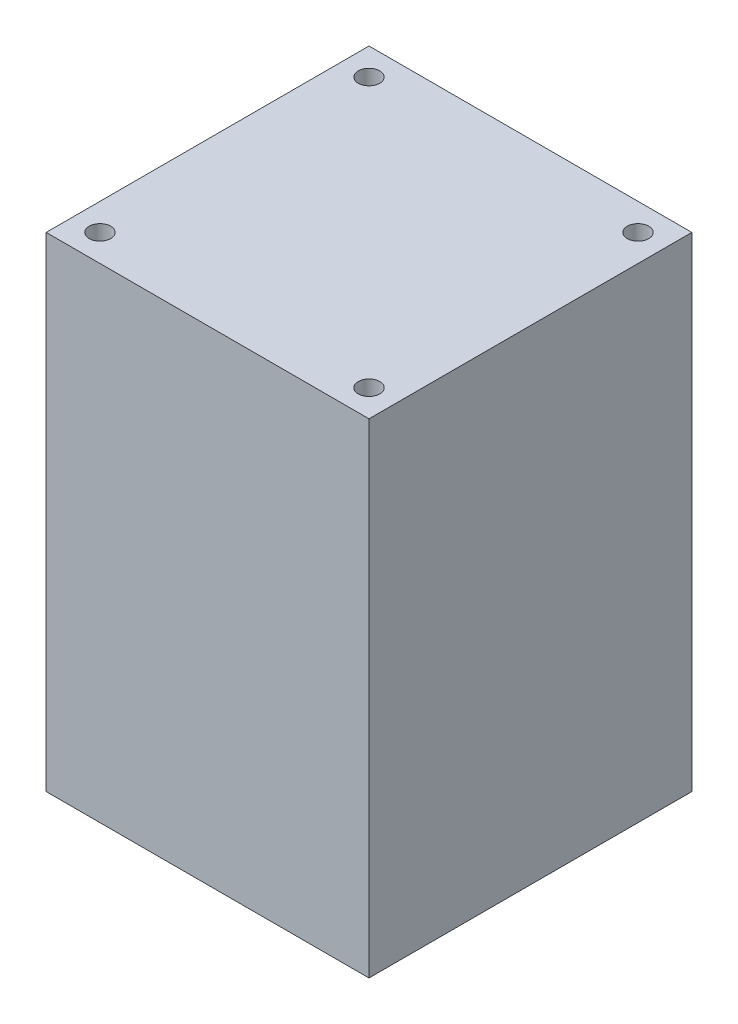
SolidWorks part; units mm, degrees
ref_plane "Front Plane" through (0, 0, 0) normal (0, 0, 1) x (1, 0, 0)
ref_plane "Top Plane" through (0, 0, 0) normal (0, 1, 0) x (1, 0, 0)
ref_plane "Right Plane" through (0, 0, 0) normal (1, 0, 0) x (0, 0, -1)
sketch "Sketch1" plane through (0, 0, 0) normal (0, 1, 0) x (1, 0, 0)
  line L1 (-30, 30) -> (30, 30)
  line L2 (-30, 30) -> (-30, -30)
  line L3 (-30, -30) -> (30, -30)
  line L4 (30, 30) -> (30, -30)
  line L5 (-30, 30) -> (30, -30) construction
  line L6 (-30, -30) -> (30, 30) construction
  point P0 (0, 0)
  dimension "D1" = 60
  dimension "D2" = 60
extrude "Boss-Extrude1" add sketch "Sketch1" along normal blind 90
sketch "Sketch2" plane through (0, 90, 0) normal (0, 1, 0) x (1, 0, 0)
  line L0 (0, -33) -> (0, 33) construction
  line L1 (-33, 0) -> (33, 0) construction
  circle A0 centre (-25, 25) radius 2
  dimension "D2" = 4
  dimension "D1" = 25
  dimension "D3" = 25
extrude "Cut-Extrude1" cut sketch "Sketch2" against normal blind 10
mirror "Mirror1" about plane through (0, 0, 0) normal (1, 0, 0) of "Cut-Extrude1"
mirror "Mirror2" about plane through (0, 0, 0) normal (0, 0, 1) of "Mirror1", "Cut-Extrude1"
